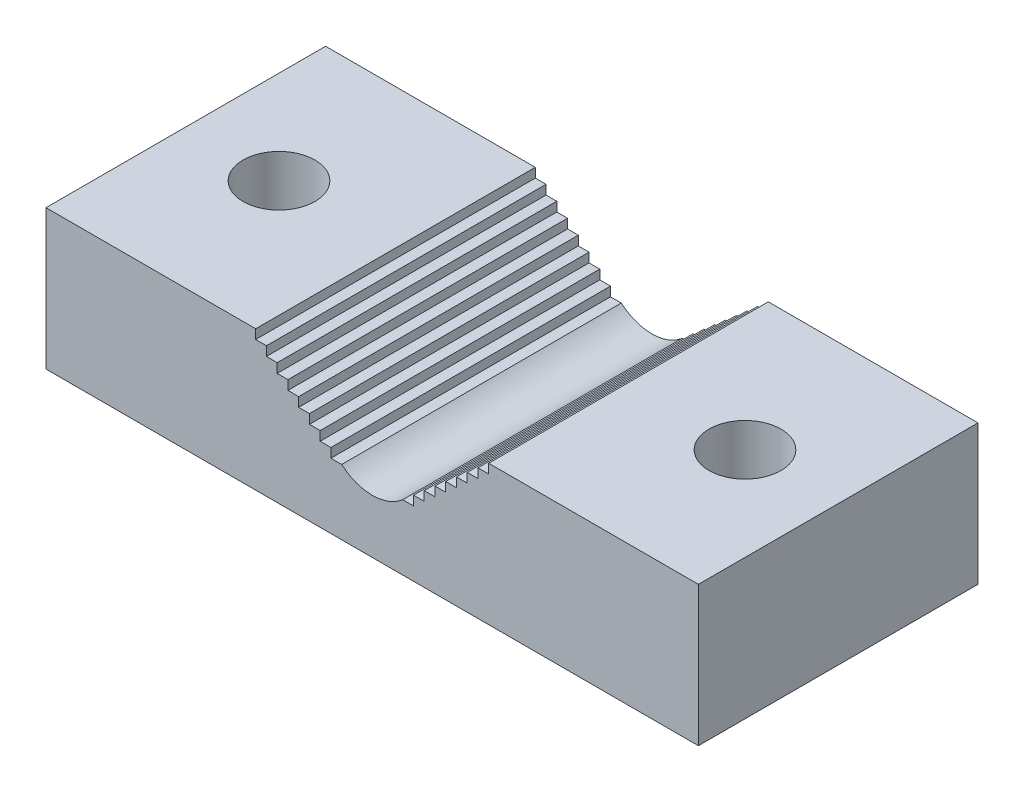
SolidWorks part; units mm, degrees
material "6061-T6 (SS)"
ref_plane "Front Plane" through (0, 0, 0) normal (0, 0, 1) x (1, 0, 0)
ref_plane "Top Plane" through (0, 0, 0) normal (0, 1, 0) x (1, 0, 0)
ref_plane "Right Plane" through (0, 0, 0) normal (1, 0, 0) x (0, 0, -1)
sketch "Sketch1" plane through (0, 0, 0) normal (0, 0, 1) x (1, 0, 0)
  line L0 (-44.45, 0) -> (44.45, 0)
  line L1 (44.45, 0) -> (44.45, 19.05)
  line L2 (44.45, 19.05) -> (-44.45, 19.05)
  line L3 (-44.45, 19.05) -> (-44.45, 0)
  point P3 (0, 0)
  dimension "D1" = 19.05
  dimension "D2" = 88.9
extrude "Boss-Extrude1" add sketch "Sketch1" against normal blind 38.1
sketch "Sketch2" plane through (0, 0, 0) normal (0, 0, 1) x (1, 0, 0)
  line L0 (-15.875, 19.05) -> (-4.1606, 8.89) construction
  line L1 (-15.875, 19.05) -> (0, 19.05)
  line L2 (44.45, 19.05) -> (-44.45, 19.05) construction
  line L3 (15.875, 19.05) -> (4.1606, 8.89) construction
  line L4 (15.875, 19.05) -> (0, 19.05)
  line L5 (-15.875, 19.05) -> (-15.875, 17.78)
  line L6 (-15.875, 17.78) -> (-14.4107, 17.78)
  line L7 (-14.4107, 17.78) -> (-14.4107, 16.51)
  line L8 (-14.4107, 16.51) -> (-12.9464, 16.51)
  line L9 (-12.9464, 16.51) -> (-12.9464, 15.24)
  line L10 (-12.9464, 15.24) -> (-11.4821, 15.24)
  line L11 (-11.4821, 15.24) -> (-11.4821, 13.97)
  line L12 (-11.4821, 13.97) -> (-10.0178, 13.97)
  line L13 (-10.0178, 13.97) -> (-10.0178, 12.7)
  line L14 (-10.0178, 12.7) -> (-8.5535, 12.7)
  line L15 (-8.5535, 12.7) -> (-8.5535, 11.43)
  line L16 (-8.5535, 11.43) -> (-7.0892, 11.43)
  line L17 (-7.0892, 11.43) -> (-7.0892, 10.16)
  line L18 (-7.0892, 10.16) -> (-5.6249, 10.16)
  line L19 (-5.6249, 10.16) -> (-5.6249, 8.89)
  line L20 (-5.6249, 8.89) -> (-4.1606, 8.89)
  line L21 (0, 19.05) -> (0, 0) construction
  line L24 (5.6249, 8.89) -> (4.1606, 8.89)
  line L25 (5.6249, 10.16) -> (5.6249, 8.89)
  line L26 (7.0892, 10.16) -> (5.6249, 10.16)
  line L27 (7.0892, 11.43) -> (7.0892, 10.16)
  line L28 (8.5535, 11.43) -> (7.0892, 11.43)
  line L29 (8.5535, 12.7) -> (8.5535, 11.43)
  line L30 (10.0178, 12.7) -> (8.5535, 12.7)
  line L31 (10.0178, 13.97) -> (10.0178, 12.7)
  line L32 (11.4821, 13.97) -> (10.0178, 13.97)
  line L33 (11.4821, 15.24) -> (11.4821, 13.97)
  line L34 (12.9464, 15.24) -> (11.4821, 15.24)
  line L35 (12.9464, 16.51) -> (12.9464, 15.24)
  line L36 (14.4107, 16.51) -> (12.9464, 16.51)
  line L37 (14.4107, 17.78) -> (14.4107, 16.51)
  line L38 (15.875, 17.78) -> (14.4107, 17.78)
  line L39 (15.875, 19.05) -> (15.875, 17.78)
  arc A0 (4.1606, 8.89) -> (-4.1606, 8.89) centre (0, 13.6871) cw
  point P7 (0, 19.05)
  dimension "D1" = 6.35
  dimension "D2" = 31.75
  dimension "D4" = 1.27
extrude "Cut-Extrude1" cut sketch "Sketch2" against normal up to next
sketch "Sketch3" plane through (0, 0, 0) normal (0, 0, 1) x (1, 0, 0)
  circle A0 centre (0, 24.151) radius 14.2875
  dimension "D1" = 28.575
hole_wizard "3/8 Clearance Hole1" positions "Sketch6" profile "Sketch5" hole size "3/8" standard "ANSI Inch" end condition through all
sketch "Sketch6" plane through (0, 19.05, 0) normal (0, 1, 0) x (1, 0, 0)
  line L1 (-44.45, 38.1) -> (-44.45, 0) construction
  line L3 (44.45, 38.1) -> (44.45, 0) construction
  point P0 (-31.75, 19.05)
  point P2 (31.75, 19.05)
  point P10 (-44.45, 19.05)
  point P16 (44.45, 19.05)
  dimension "D1" = 12.7
  dimension "D2" = 12.7
sketch "Sketch5" plane through (-31.75, 19.05, -19.05) normal (1, 0, 0) x (0, 0, 1)
  line L0 (0, 0) -> (0, 19.05)
  line L1 (0, 19.05) -> (4.9022, 19.05)
  line L2 (4.9022, 19.05) -> (4.9022, 0)
  line L5 (4.9022, 0) -> (0, 0)
  line L11 (0, -6.35) -> (0, 107.95) construction
  dimension "Thru Hole Dia." = 9.8044
  dimension "Thru Hole Depth" = 19.05
